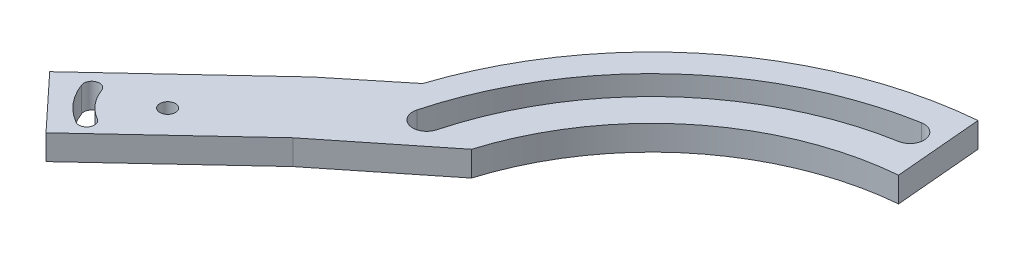
SolidWorks part; units mm, degrees
ref_plane "Front Plane" through (0, 0, 0) normal (0, 0, 1) x (1, 0, 0)
ref_plane "Top Plane" through (0, 0, 0) normal (0, 1, 0) x (1, 0, 0)
ref_plane "Right Plane" through (0, 0, 0) normal (1, 0, 0) x (0, 0, -1)
sketch "Sketch1" plane through (0, 0, 0) normal (0, 1, 0) x (1, 0, 0)
  circle A0 centre (0, 0) radius 57.5
  dimension "D1" = 115
extrude "Boss-Extrude1" add sketch "Sketch1" along normal blind 4
sketch "Sketch2" plane through (0, 0, 0) normal (0, 1, 0) x (1, 0, 0)
  line L0 (0, 0) -> (-57.5, 0) construction
  line L5 (-57.5, 0) -> (-77.9779, -19.096) construction
  line L6 (-77.9779, -19.096) -> (-57.5, 0)
  line L7 (-77.9779, -19.096) -> (-86.1619, -10.3197)
  line L9 (-86.1619, -10.3197) -> (-64.3468, 10.0232)
  line L10 (-64.3468, 10.0232) -> (-44.9244, 25.8036)
  line L11 (-44.9244, 25.8036) -> (-44.9244, 0)
  line L12 (-44.9244, 0) -> (-57.5, 0)
  circle A0 centre (0, 0) radius 57.5 construction
  dimension "D1" = 12
  dimension "D2" = 28
  dimension "D3" = 223
extrude "Boss-Extrude2" add sketch "Sketch2" along normal blind 4
sketch "Sketch3" plane through (0, 0, 0) normal (0, 1, 0) x (1, 0, 0)
  line L0 (0, 0) -> (-57.5, 0) construction
  line L1 (-47.0889, 12.6174) -> (-51.4356, 13.7821) construction
  line L2 (-8.4653, 48.0094) -> (-9.2468, 52.441) construction
  circle A0 centre (0, 0) radius 51 construction
  arc A1 (-51.4356, 13.7821) -> (-9.2468, 52.441) centre (0, 0) cw
  arc A2 (-47.0889, 12.6174) -> (-8.4653, 48.0094) centre (0, 0) cw
  arc A3 (-51.4356, 13.7821) -> (-47.0889, 12.6174) centre (-49.2622, 13.1998) ccw
  arc A4 (-9.2468, 52.441) -> (-8.4653, 48.0094) centre (-8.8561, 50.2252) cw
  dimension "D1" = 102
  dimension "D2" = 53.25
  dimension "D3" = 48.75
  dimension "D4" = 65
  dimension "D5" = 15
extrude "Cut-Extrude1" cut sketch "Sketch3" along normal through all
sketch "Sketch4" plane through (0, 0, 0) normal (0, 1, 0) x (1, 0, 0)
  line L0 (0, 0) -> (-57.5, 0)
  line L1 (0, 0) -> (-5.0115, 57.2812)
  circle A0 centre (0, 0) radius 57.5 construction
  arc A1 (-57.5, 0) -> (-5.0115, 57.2812) centre (0, 0) ccw
  dimension "D1" = 85
extrude "Cut-Extrude2" cut sketch "Sketch4" along normal through all
sketch "Sketch5" plane through (0, 0, 0) normal (0, 1, 0) x (1, 0, 0)
  circle A0 centre (0, 0) radius 43.5
  dimension "D1" = 87
extrude "Cut-Extrude3" cut sketch "Sketch5" along normal through all
sketch "Sketch7" plane through (0, 0, 0) normal (0, 1, 0) x (1, 0, 0)
  line L0 (-57.5, 0) -> (-41.6039, 12.7028)
  line L1 (-41.6039, 12.7028) -> (-43.5, 0)
  line L2 (-43.5, 0) -> (-57.5, 0)
  arc A0 (-3.7913, 43.3345) -> (-43.5, 0) centre (0, 0) ccw construction
extrude "Cut-Extrude7" cut sketch "Sketch7" along normal through all
sketch "Sketch9" plane through (0, 4, 0) normal (0, 1, 0) x (1, 0, 0)
  line L0 (-77.9779, -19.096) -> (-70.5863, -6.5476)
  line L1 (-77.9779, -19.096) -> (-79.0549, -18.4615)
  line L2 (-70.5863, -6.5476) -> (-71.6634, -5.9132)
  line L3 (-79.0549, -18.4615) -> (-71.6634, -5.9132)
  line L5 (-77.9779, -19.096) -> (-57.5, 0) construction
  line L6 (-86.1619, -10.3197) -> (-77.9779, -19.096) construction
  circle A0 centre (-76.485, -14.0986) radius 1.25
  circle A1 centre (-71.6634, -5.9132) radius 1.25
  dimension "D1" = 2.5
  dimension "D2" = 9.5
  dimension "D3" = 16.5
  dimension "D4" = 4.5
  dimension "D5" = 1.25
extrude "Cut-Extrude10" cut sketch "Sketch9" against normal through all contours A1 | A0
sketch "Sketch10" plane through (0, 4, 0) normal (0, 1, 0) x (1, 0, 0)
  line L0 (-75.7884, -13.0579) -> (-77.0384, -15.2229) construction
  line L1 (-81.7651, -9.5899) -> (-79.4159, -8.7348) construction
  line L2 (-77.9779, -19.096) -> (-57.5, 0) construction
  arc A0 (-75.7884, -13.0579) -> (-79.4159, -8.7348) centre (-71.6634, -5.9132) cw
  arc A1 (-77.0384, -15.2229) -> (-81.7651, -9.5899) centre (-71.6634, -5.9132) cw
  arc A2 (-79.4159, -8.7348) -> (-81.7651, -9.5899) centre (-80.5905, -9.1624) ccw
  arc A3 (-77.0384, -15.2229) -> (-75.7884, -13.0579) centre (-76.4134, -14.1404) ccw
  dimension "D1" = 2.5
  dimension "D3" = 40
  dimension "D4" = 17
extrude "Cut-Extrude14" cut sketch "Sketch10" against normal through all
